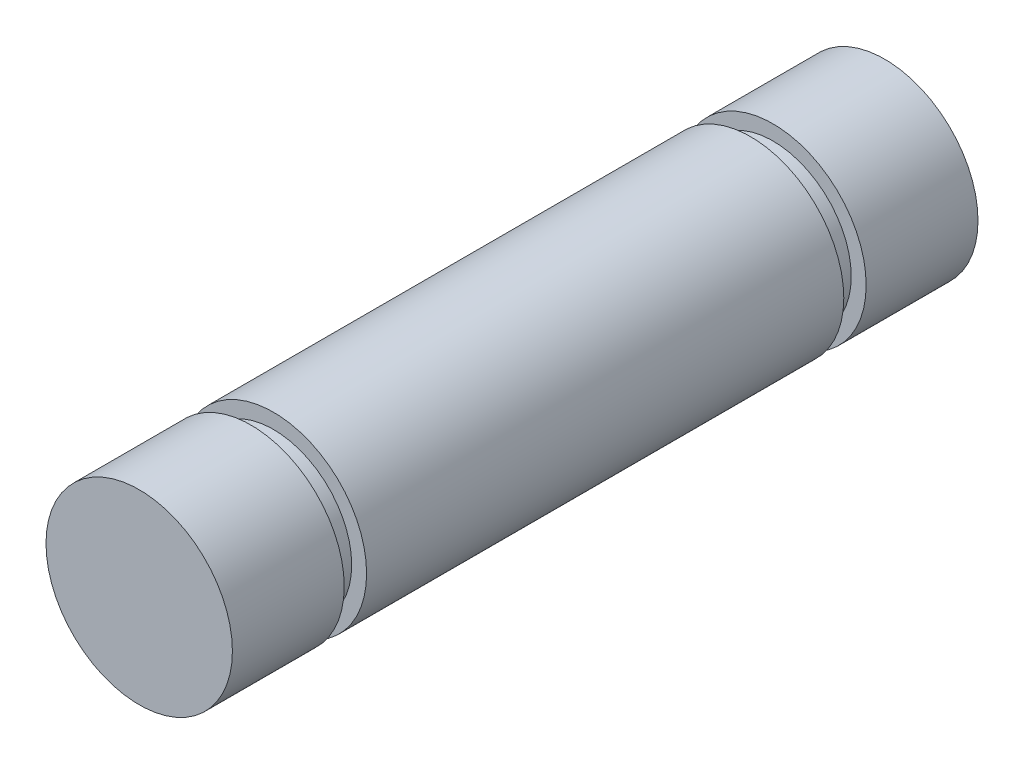
SolidWorks part; units mm, degrees
ref_plane "Front Plane" through (0, 0, 0) normal (0, 0, 1) x (1, 0, 0)
ref_plane "Top Plane" through (0, 0, 0) normal (0, 1, 0) x (1, 0, 0)
ref_plane "Right Plane" through (0, 0, 0) normal (1, 0, 0) x (0, 0, -1)
sketch "Sketch1" plane through (0, 0, 0) normal (0, 0, 1) x (1, 0, 0)
  circle A0 centre (0, 0) radius 3.175
  dimension "D1" = 6.35
extrude "Boss-Extrude1" add sketch "Sketch1" along normal mid plane 25.4
sketch "Sketch2" plane through (0, 0, 0) normal (0, 1, 0) x (1, 0, 0)
  line L0 (3.175, -12.7) -> (3.175, 12.7) construction
  line L1 (3.175, 8.89) -> (2.667, 8.89)
  line L2 (3.175, 8.89) -> (3.175, 8.128)
  line L3 (3.175, 8.128) -> (2.667, 8.128)
  line L4 (2.667, 8.89) -> (2.667, 8.128)
  line L5 (3.175, 12.7) -> (-3.175, 12.7) construction
  line L6 (3.175, -8.128) -> (2.667, -8.128)
  line L7 (3.175, -8.128) -> (3.175, -8.89)
  line L8 (3.175, -8.89) -> (2.667, -8.89)
  line L9 (2.667, -8.128) -> (2.667, -8.89)
  line L10 (-3.175, -12.7) -> (3.175, -12.7) construction
  point P10 (2.667, 8.509)
  dimension "D1" = 0.508
  dimension "D2" = 0.508
  dimension "D3" = 0.762
  dimension "D4" = 0.762
  dimension "D5" = 3.81
  dimension "D6" = 3.81
ref_axis "Axis1" through (0, 0, 12.7) along (0, 0, -1)
revolve "Cut-Revolve1" cut sketch "Sketch2" angle 360 about axis through (0, 0, 12.7) along (0, 0, -1)
